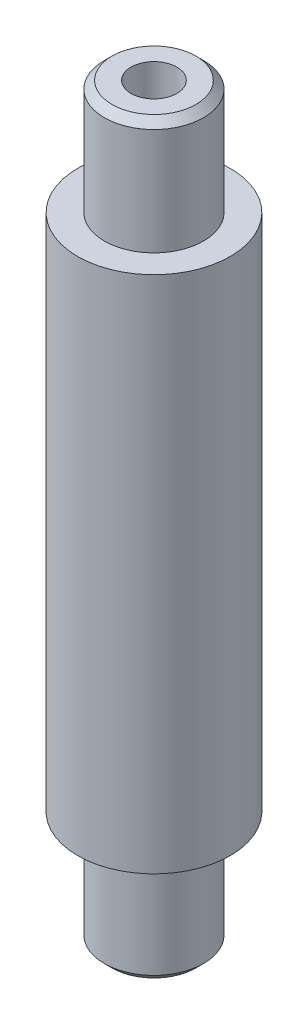
SolidWorks part; units mm, degrees
ref_plane "정면" through (0, 0, 0) normal (0, 0, 1) x (1, 0, 0)
ref_plane "윗면" through (0, 0, 0) normal (0, 1, 0) x (1, 0, 0)
ref_plane "우측면" through (0, 0, 0) normal (1, 0, 0) x (0, 0, -1)
sketch "스케치1" plane through (0, 0, 0) normal (0, 1, 0) x (1, 0, 0)
  circle A0 centre (0, 0) radius 10
  dimension "D1" = 20
extrude "보스-돌출1" add sketch "스케치1" along normal mid plane 68
sketch "스케치2" plane through (0, 0, 0) normal (0, 1, 0) x (1, 0, 0)
  circle A0 centre (0, 0) radius 6.5
  point P3 (3.6577, -4.6945)
  dimension "D1" = 13
extrude "보스-돌출2" add sketch "스케치2" along normal mid plane 98
chamfer "모따기1" distance 1 angle 45 2 edges at (0, -49, 6.5) (0, 49, 6.5)
sketch "스케치3" plane through (0, 49, 0) normal (0, 1, 0) x (1, 0, 0)
  circle A0 centre (0, 0) radius 3
  dimension "D1" = 6
extrude "컷-돌출1" cut sketch "스케치3" against normal blind 14
mirror "대칭 복사1" about plane through (0, 0, 0) normal (0, 1, 0) of "컷-돌출1"
chamfer "모따기2" distance 1 angle 45 2 edges at (0, 35, 3) (0, -35, 3)
